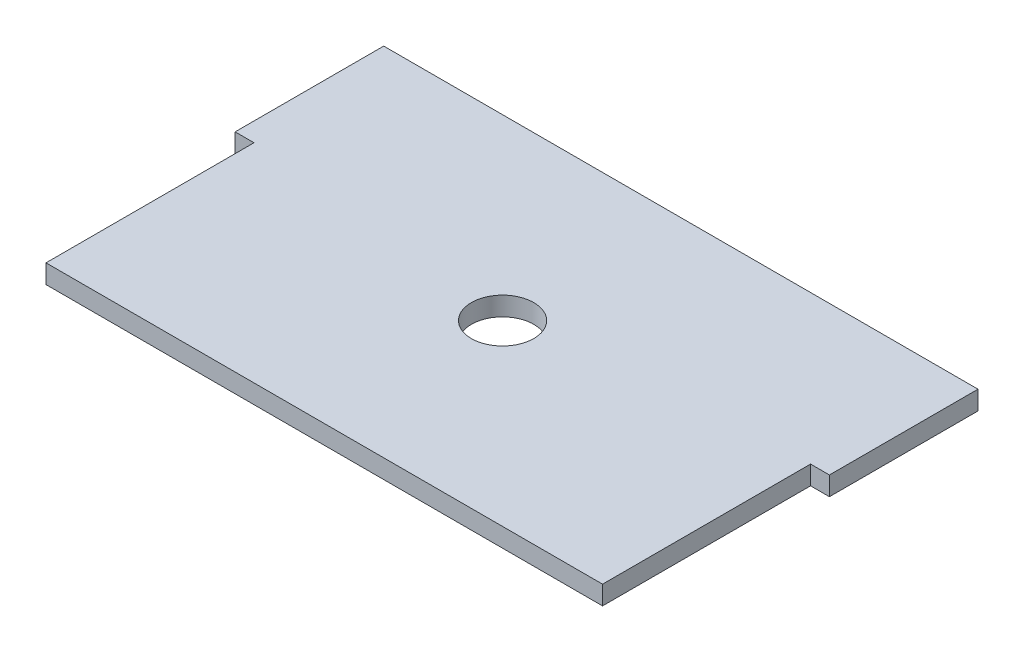
SolidWorks part; units mm, degrees
material "FiberBoard"
ref_plane "Front Plane" through (0, 0, 0) normal (0, 0, 1) x (1, 0, 0)
ref_plane "Top Plane" through (0, 0, 0) normal (0, 1, 0) x (1, 0, 0)
ref_plane "Right Plane" through (0, 0, 0) normal (1, 0, 0) x (0, 0, -1)
sketch "Sketch1" plane through (0, 0, 0) normal (0, 1, 0) x (1, 0, 0)
  line L1 (0, 0) -> (100, 0)
  line L2 (0, 0) -> (0, -60)
  line L3 (0, -60) -> (100, -60)
  line L4 (100, 0) -> (100, -60)
  dimension "D1" = 100
  dimension "D2" = 60
extrude "Boss-Extrude1" add sketch "Sketch1" along normal blind 3.175
sketch "Sketch2" plane through (0, 3.175, 0) normal (0, 1, 0) x (1, 0, 0)
  line L1 (3.175, -25) -> (3.175, -35)
  line L2 (0, 0) -> (3.175, 0) construction
  line L3 (0, 0) -> (0, -25) construction
  line L4 (0, -25) -> (3.175, -25) construction
  line L5 (3.175, 0) -> (3.175, -25) construction
  line L6 (0, -60) -> (3.175, -60)
  line L7 (0, -60) -> (0, -45)
  line L9 (3.175, -60) -> (3.175, -35)
  line L10 (100, 0) -> (96.825, 0) construction
  line L11 (100, 0) -> (100, -25) construction
  line L12 (100, -25) -> (96.825, -25)
  line L13 (96.825, 0) -> (96.825, -25) construction
  line L14 (100, -60) -> (96.825, -60)
  line L15 (100, -60) -> (100, -45)
  line L17 (96.825, -60) -> (96.825, -35)
  line L18 (0, -25) -> (0, -45)
  line L19 (96.825, -25) -> (96.825, -35)
  line L20 (100, -25) -> (100, -45)
  line L21 (3.175, -25) -> (0, -25)
  dimension "D1" = 25
  dimension "D2" = 3.175
extrude "Cut-Extrude1" cut sketch "Sketch2" against normal blind 3.175
hole_wizard "Tap Drill for M12x1.5 Tap1" positions "Sketch3" profile "Sketch4" hole size "M12x1.5" standard "ANSI Metric" end condition through all
sketch "Sketch3" plane through (0, 3.175, 0) normal (0, 1, 0) x (1, 0, 0)
  line L3 (100, 0) -> (0, 0) construction
  line L4 (50, 0) -> (50, -60)
  line L5 (3.175, -60) -> (96.825, -60) construction
  point P0 (50, -30)
  point P24 (50, -30)
sketch "Sketch4" plane through (50, 3.175, 30) normal (1, 0, 0) x (0, 0, 1)
  line L0 (0, 0) -> (0, 3.175)
  line L1 (0, 3.175) -> (5.25, 3.175)
  line L2 (5.25, 3.175) -> (5.25, 0)
  line L5 (5.25, 0) -> (0, 0)
  line L11 (0, -6.35) -> (0, 107.95) construction
  dimension "Thru Hole Dia." = 10.5
  dimension "Thru Hole Depth" = 3.175
